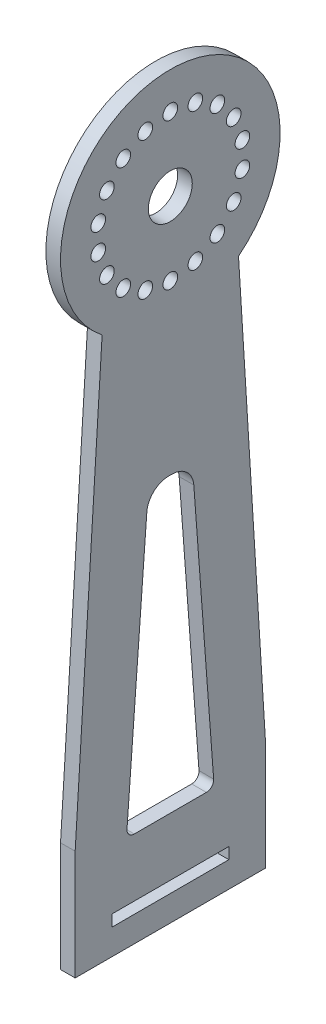
SolidWorks part; units mm, degrees
material "Plástico personalizado"
ref_plane "Plano frontal" through (0, 0, 0) normal (0, 0, 1) x (1, 0, 0)
ref_plane "Plano superior" through (0, 0, 0) normal (0, 1, 0) x (1, 0, 0)
ref_plane "Plano direito" through (0, 0, 0) normal (1, 0, 0) x (0, 0, -1)
sketch "Esboço1" plane through (0, 0, 0) normal (1, 0, 0) x (0, 0, -1)
  line L0 (-13, -71) -> (-13, -86)
  line L1 (-13, -86) -> (0, -86)
  line L3 (0, 15) -> (0, -86)
  arc A0 (0, 15) -> (-9.3165, -11.756) centre (0, 0) ccw
  spline S0 degree 1 poles (-9.3165, -11.756) (-13, -71) knots 0 0 1 1
  dimension "D1" = 30
  dimension "D4" = 15
  dimension "D5" = 86
extrude "Ressalto-extrusão1" add sketch "Esboço1" along normal blind 2
mirror "Espelhar1" about plane through (2, 15, 0) normal (0, 0, 1) of "Ressalto-extrusão1"
sketch "Esboço2" plane through (2, 0, 0) normal (1, 0, 0) x (0, 0, -1)
  circle A0 centre (0, 0) radius 3
  circle A1 centre (0, -10) radius 1
  dimension "D1" = 6
  dimension "D3" = 2
  dimension "D2" = 10
extrude "Corte-extrusão1" cut sketch "Esboço2" against normal blind 2
pattern_circular "PadrãoCircular1" count 18 over 360 about axis through (0, 0, 0) along (1, 0, 0) of "Corte-extrusão1"
sketch "Esboço3" plane through (2, 0, 0) normal (1, 0, 0) x (0, 0, -1)
  line L0 (-4.9222, -73) -> (4.9222, -73)
  line L1 (5.9194, -71.9252) -> (3.2082, -35.7756)
  line L2 (0.2166, -33) -> (-0.2166, -33)
  line L3 (-3.2082, -35.7756) -> (-5.9194, -71.9252)
  line L5 (-13, -86) -> (13, -86) construction
  line L6 (-8, -80.9386) -> (8, -80.9386)
  line L7 (-8, -80.9386) -> (-8, -82.5)
  line L8 (-8, -82.5) -> (8, -82.5)
  line L9 (8, -80.9386) -> (8, -82.5)
  line L10 (-8, -80.9386) -> (8, -82.5) construction
  line L11 (-8, -82.5) -> (8, -80.9386) construction
  arc A0 (0.2166, -33) -> (3.2082, -35.7756) centre (0.2166, -36) cw
  arc A1 (-0.2166, -33) -> (-3.2082, -35.7756) centre (-0.2166, -36) ccw
  arc A2 (4.9222, -73) -> (5.9194, -71.9252) centre (4.9222, -72) ccw
  arc A3 (-4.9222, -73) -> (-5.9194, -71.9252) centre (-4.9222, -72) cw
  point P6 (3, -33)
  point P9 (-3, -33)
  point P12 (6, -73)
  point P15 (-6, -73)
  point P16 (0, -81.7193)
  point P23 (0, -86)
  point P24 (0, -73)
  point P25 (0, -33)
  dimension "D4" = 3
  dimension "D5" = 1
  dimension "D1" = 12
  dimension "D2" = 6
  dimension "D3" = 40
  dimension "D6" = 16
  dimension "D7" = 3.5
extrude "Corte-extrusão2" cut sketch "Esboço3" against normal blind 2
